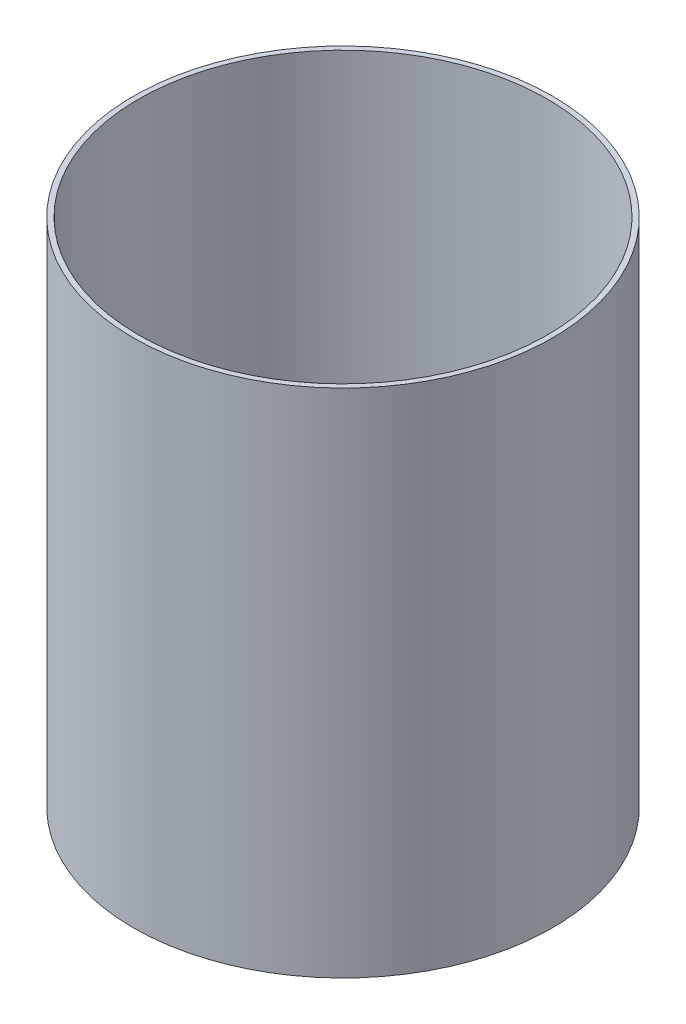
SolidWorks part; units mm, degrees
ref_plane "Plano frontal" through (0, 0, 0) normal (0, 0, 1) x (1, 0, 0)
ref_plane "Plano superior" through (0, 0, 0) normal (0, 1, 0) x (1, 0, 0)
ref_plane "Plano direito" through (0, 0, 0) normal (1, 0, 0) x (0, 0, -1)
sketch "Esboço1" plane through (0, 0, 0) normal (0, 1, 0) x (1, 0, 0)
  circle A0 centre (0, 0) radius 102.5
  circle A1 centre (0, 0) radius 100
  dimension "D1" = 205
  dimension "D2" = 200
extrude "Ressalto-extrusão1" add sketch "Esboço1" along normal blind 250
